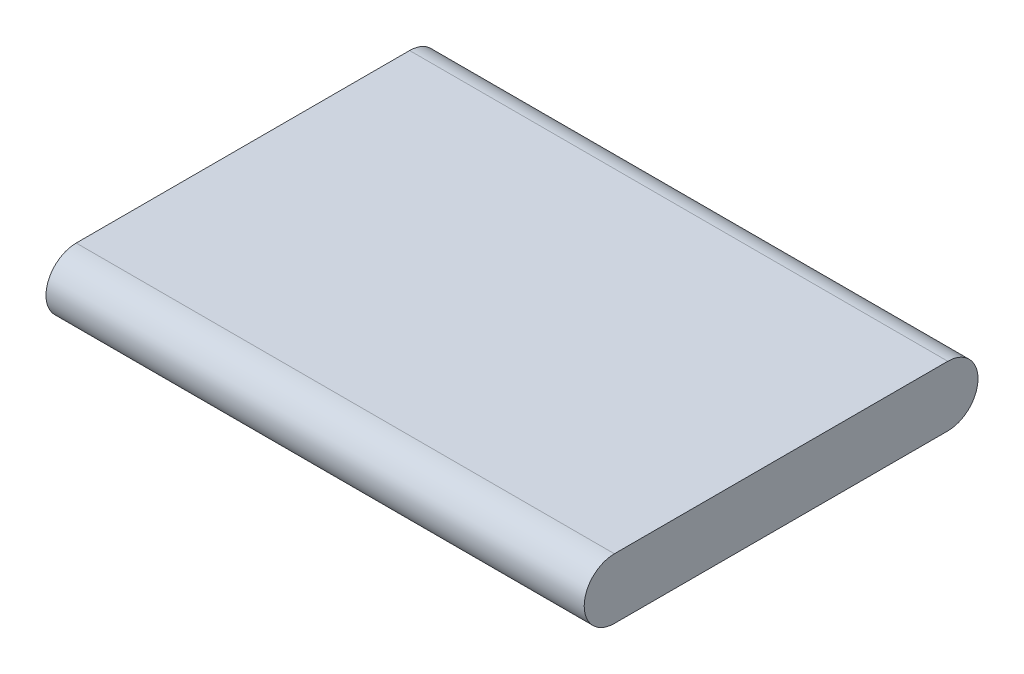
SolidWorks part; units mm, degrees
ref_plane "Front Plane" through (0, 0, 0) normal (0, 0, 1) x (1, 0, 0)
ref_plane "Top Plane" through (0, 0, 0) normal (0, 1, 0) x (1, 0, 0)
ref_plane "Right Plane" through (0, 0, 0) normal (1, 0, 0) x (0, 0, -1)
sketch "Sketch1" plane through (0, 0, 0) normal (1, 0, 0) x (0, 0, -1)
  line L0 (-10.8135, 0) -> (14.5865, 0) construction
  line L5 (-10.8135, 2.3) -> (14.5865, 2.3)
  line L6 (-10.8135, -2.3) -> (14.5865, -2.3)
  arc A0 (-10.8135, 2.3) -> (-10.8135, -2.3) centre (-10.8135, 0) ccw
  arc A1 (14.5865, -2.3) -> (14.5865, 2.3) centre (14.5865, 0) ccw
  point P2 (1.8865, 0)
  point P8 (-13.1135, 0)
  point P9 (16.8865, 0)
  dimension "D1" = 4.6
  dimension "D2" = 30
extrude "Boss-Extrude1" add sketch "Sketch1" along normal blind 41
